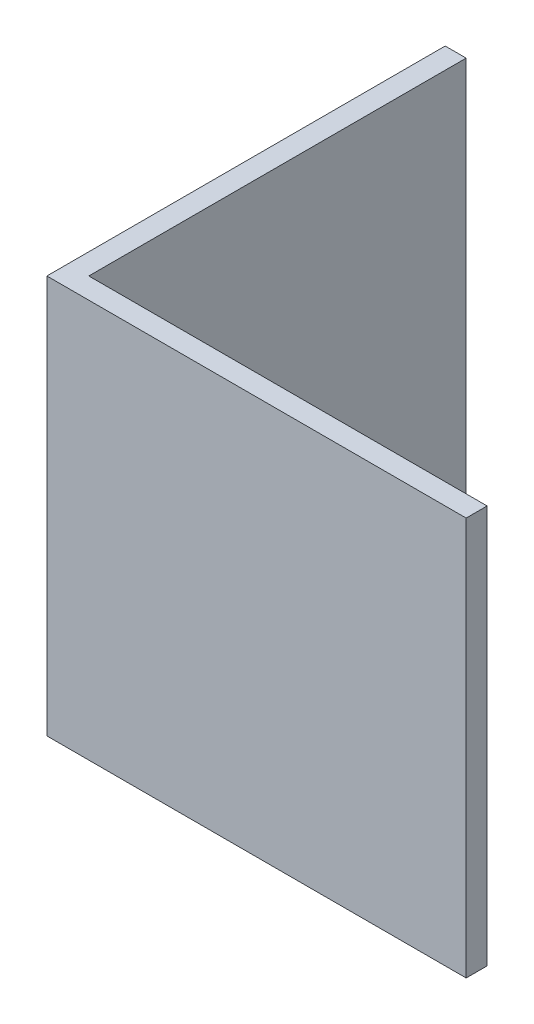
SolidWorks part; units mm, degrees
material "1060 Сплав"
ref_plane "Спереди" through (0, 0, 0) normal (0, 0, 1) x (1, 0, 0)
ref_plane "Сверху" through (0, 0, 0) normal (0, 1, 0) x (1, 0, 0)
ref_plane "Справа" through (0, 0, 0) normal (1, 0, 0) x (0, 0, -1)
sketch "Эскиз1" plane through (0, 0, 0) normal (0, 1, 0) x (1, 0, 0)
  line L0 (0, 0) -> (0, 20)
  line L1 (0, 20) -> (1, 20)
  line L2 (1, 20) -> (1, 1)
  line L3 (1, 1) -> (20, 1)
  line L4 (20, 1) -> (20, 0)
  line L5 (20, 0) -> (0, 0)
  dimension "D1" = 1
  dimension "D2" = 20
extrude "Бобышка-Вытянуть1" add sketch "Эскиз1" along normal blind 19
sketch "Эскиз4" plane through (0, 0, -20) normal (0, 0, -1) x (-1, 0, 0)
  line L4 (-1, 0) -> (0, 0)
  line L5 (0, 0) -> (0, 19)
  line L6 (0, 19) -> (-1, 19)
  line L7 (-1, 19) -> (-1, 0)
  line L8 (-1, 0) -> (0, 0)
  line L9 (0, 0) -> (0, 19)
  line L10 (0, 19) -> (-1, 19)
  line L11 (-1, 19) -> (-1, 0)
  dimension "D1" = 0
extrude "Вырез-Вытянуть2" cut sketch "Эскиз4" against normal blind 1
